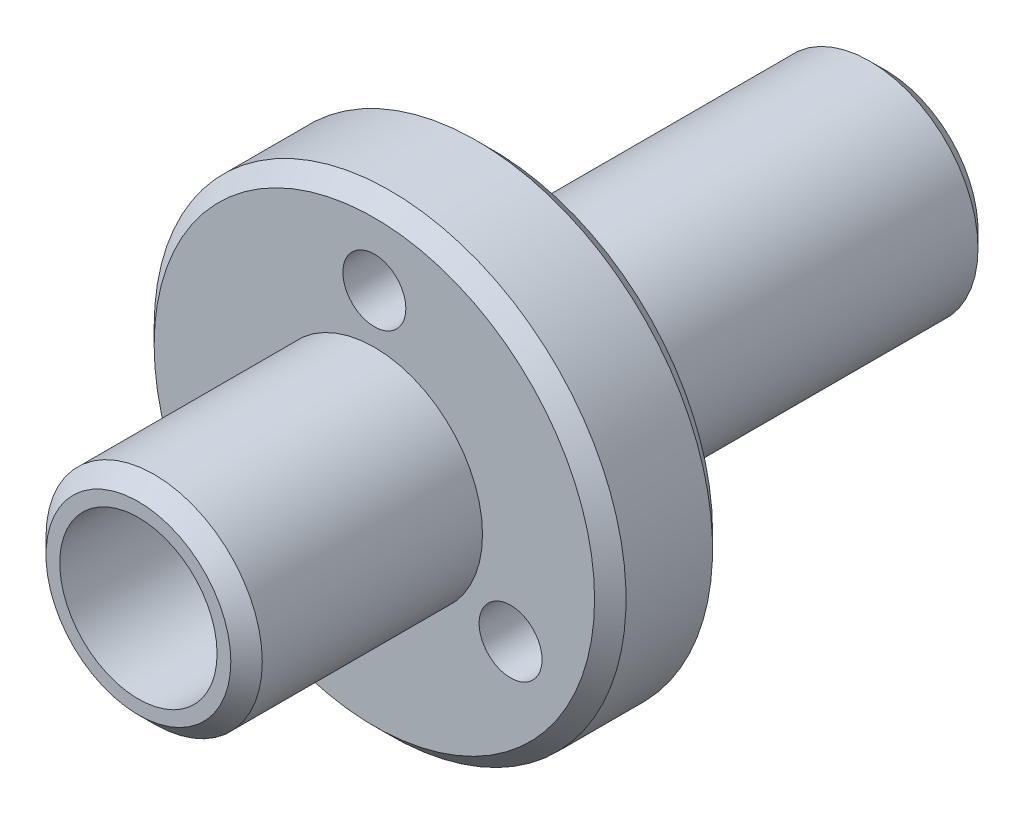
SolidWorks part; units mm, degrees
ref_plane "Front Plane" through (0, 0, 0) normal (0, 0, 1) x (1, 0, 0)
ref_plane "Top Plane" through (0, 0, 0) normal (0, 1, 0) x (1, 0, 0)
ref_plane "Right Plane" through (0, 0, 0) normal (1, 0, 0) x (0, 0, -1)
sketch "Sketch1" plane through (0, 0, 0) normal (0, 0, 1) x (1, 0, 0)
  circle A2 centre (-27.5, 59.9979) radius 2.75 construction
  circle A3 centre (-27.5, 59.9979) radius 2.75
ref_plane "Plane1" through (-27.5, 0, 0) normal (1, 0, 0) x (0, 0, -1)
sketch "Sketch2" plane through (-27.5, 0, 0) normal (1, 0, 0) x (0, 0, -1)
  line L0 (0, 59.9979) -> (2, 59.9979)
  line L1 (2, 59.9979) -> (4, 59.9979)
  line L2 (0, -108.5) -> (2, -108.5) construction
  line L3 (4, 59.9979) -> (6, 59.9979)
extrude "Boss-Extrude1" add sketch "Sketch1" against normal up to vertex (6 mm away) up to point (-27.5, 59.9979, -6)
sketch "Sketch3" plane through (0, 0, -6) normal (0, 0, -1) x (-1, 0, 0)
  circle A0 centre (27.5, 59.9979) radius 6 construction
  circle A1 centre (27.5, 59.9979) radius 6
extrude "Boss-Extrude2" add sketch "Sketch3" along normal blind 3
sketch "Sketch4" plane through (0, 0, -9) normal (0, 0, -1) x (-1, 0, 0)
  circle A0 centre (27.5, 59.9979) radius 2.75 construction
  circle A1 centre (27.5, 59.9979) radius 2.75
extrude "Boss-Extrude3" add sketch "Sketch4" along normal blind 10
hole_wizard "M2x0.4 Tapped Hole1" positions "Sketch5" profile "Sketch6" tap size "M2x0.4" standard "ANSI Metric" end condition through all
sketch "Sketch5" plane through (0, 0, -6) normal (0, 0, 1) x (1, 0, 0)
  point P0 (-24.0359, 57.9979)
  point P3 (-30.9641, 57.9979)
  point P6 (-27.5, 63.9979)
sketch "Sketch6" plane through (-24.0359, 57.9979, -6) normal (1, 0, 0) x (0, -1, 0)
  line L0 (0, 0) -> (0, 13)
  line L1 (0, 13) -> (0.8, 13)
  line L2 (0.8, 13) -> (0.8, 0)
  line L5 (0.8, 0) -> (0, 0)
  line L11 (0, -6.35) -> (0, 107.95) construction
  dimension "Thru Tap Drill Dia." = 1.6
  dimension "Thru Tap Drill Depth" = 13
cosmetic thread "Hole Thread1" parameters "D2"=2
cosmetic thread "Hole Thread2" parameters "D2"=2
cosmetic thread "Hole Thread3" parameters "D2"=2
chamfer "Chamfer1" distance 0.4 angle 45 4 edges at (-30.25, 59.9979, -19) (-24.75, 59.9979, 0) (-33.5, 59.9979, -6) (-33.5, 59.9979, -9)
sketch "Sketch7" plane through (0, 0, 0) normal (0, 0, 1) x (1, 0, 0)
  circle A6 centre (-27.5, 59.9979) radius 2 construction
  circle A7 centre (-27.5, 59.9979) radius 2
extrude "Cut-Extrude1" cut sketch "Sketch7" against normal through all
